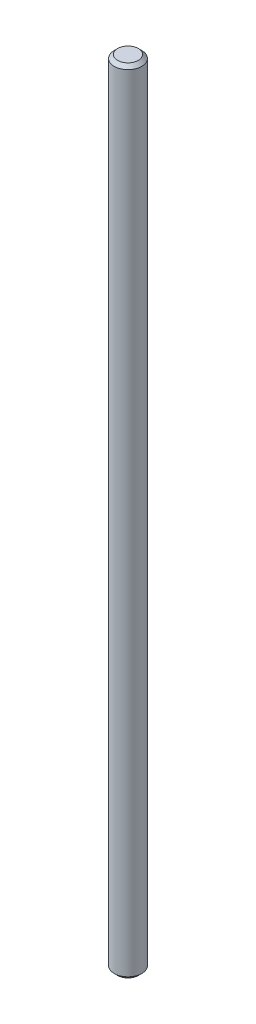
SolidWorks part; units mm, degrees
ref_plane "前视基准面" through (0, 0, 0) normal (0, 0, 1) x (1, 0, 0)
ref_plane "上视基准面" through (0, 0, 0) normal (0, 1, 0) x (1, 0, 0)
ref_plane "右视基准面" through (0, 0, 0) normal (1, 0, 0) x (0, 0, -1)
sketch "草图1" plane through (0, 0, 0) normal (0, 1, 0) x (1, 0, 0)
  circle A0 centre (0, 0) radius 4
  dimension "D1" = 8
extrude "凸台-拉伸1" add sketch "草图1" along normal blind 230
cosmetic thread "装饰螺纹线1" parameters "D2"=6.647
chamfer "倒角1" distance 1 angle 45 2 edges at (0, 0, 4) (0, 230, 4)
